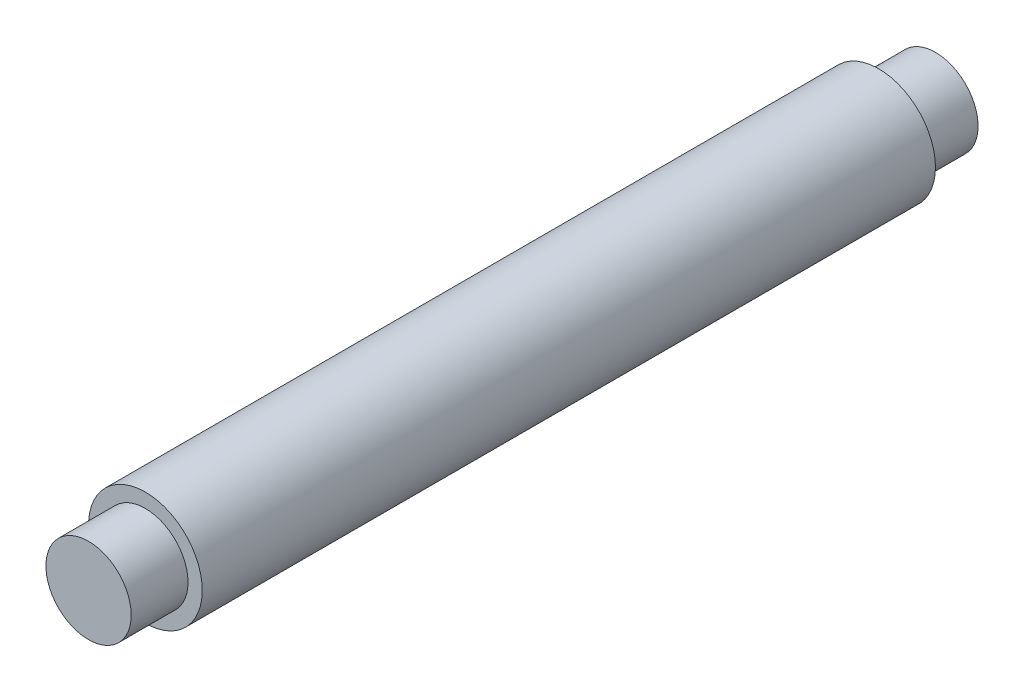
SolidWorks part; units mm, degrees
ref_plane "Front Plane" through (0, 0, 0) normal (0, 0, 1) x (1, 0, 0)
ref_plane "Top Plane" through (0, 0, 0) normal (0, 1, 0) x (1, 0, 0)
ref_plane "Right Plane" through (0, 0, 0) normal (1, 0, 0) x (0, 0, -1)
sketch "Sketch1" plane through (0, 0, 0) normal (0, 0, 1) x (1, 0, 0)
  circle A0 centre (0, 0) radius 20
extrude "Boss-Extrude1" add sketch "Sketch1" along normal blind 258
sketch "Sketch2" plane through (0, 0, 258) normal (0, 0, 1) x (1, 0, 0)
  circle A0 centre (0, 0) radius 15
extrude "Boss-Extrude2" add sketch "Sketch2" along normal blind 20
sketch "Sketch3" plane through (0, 0, 0) normal (0, 0, -1) x (-1, 0, 0)
  circle A0 centre (0, 0) radius 15
extrude "Boss-Extrude3" add sketch "Sketch3" along normal blind 20
